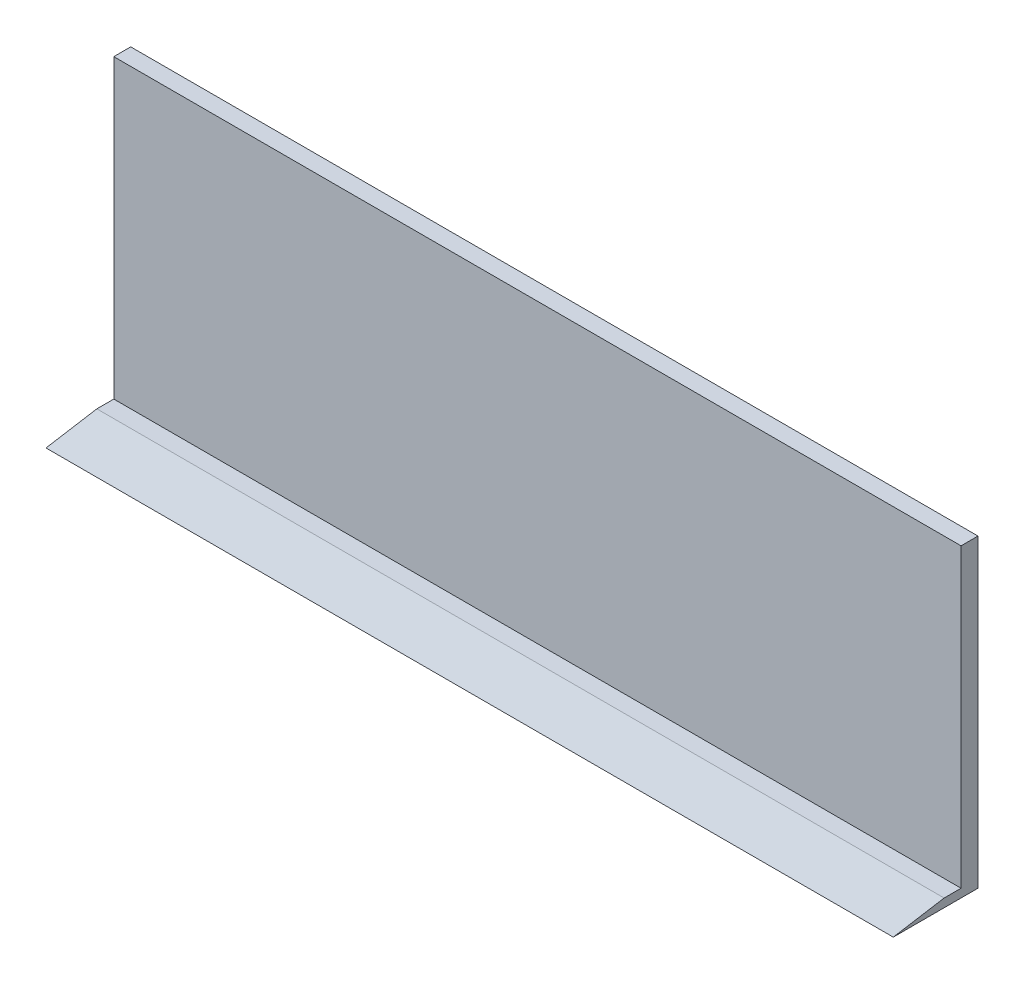
SolidWorks part; units mm, degrees
ref_plane "Plan de face" through (0, 0, 0) normal (0, 0, 1) x (1, 0, 0)
ref_plane "Plan de dessus" through (0, 0, 0) normal (0, 1, 0) x (1, 0, 0)
ref_plane "Plan de droite" through (0, 0, 0) normal (1, 0, 0) x (0, 0, -1)
sketch "Esquisse1" plane through (0, 0, 0) normal (0, 0, 1) x (1, 0, 0)
  line L1 (0, 0) -> (-250, 0)
  line L2 (0, 0) -> (0, 90)
  line L3 (0, 90) -> (-250, 90)
  line L4 (-250, 0) -> (-250, 90)
  dimension "D1" = 90
  dimension "D2" = 250
extrude "Boss.-Extru.1" add sketch "Esquisse1" along normal blind 5
sketch "Esquisse2" plane through (0, 0, 0) normal (1, 0, 0) x (0, 0, -1)
  line L0 (-5, 0) -> (-25, 0)
  line L1 (-5, 2.5) -> (-10, 2.5)
  line L3 (-5, 0) -> (-5, 90) construction
  line L4 (-10, 2.5) -> (-25, 0)
  line L5 (-5, 2.5) -> (-5, 0)
  dimension "D1" = 20
  dimension "D2" = 5
  dimension "D3" = 2.5
extrude "Boss.-Extru.2" add sketch "Esquisse2" against normal blind 250
